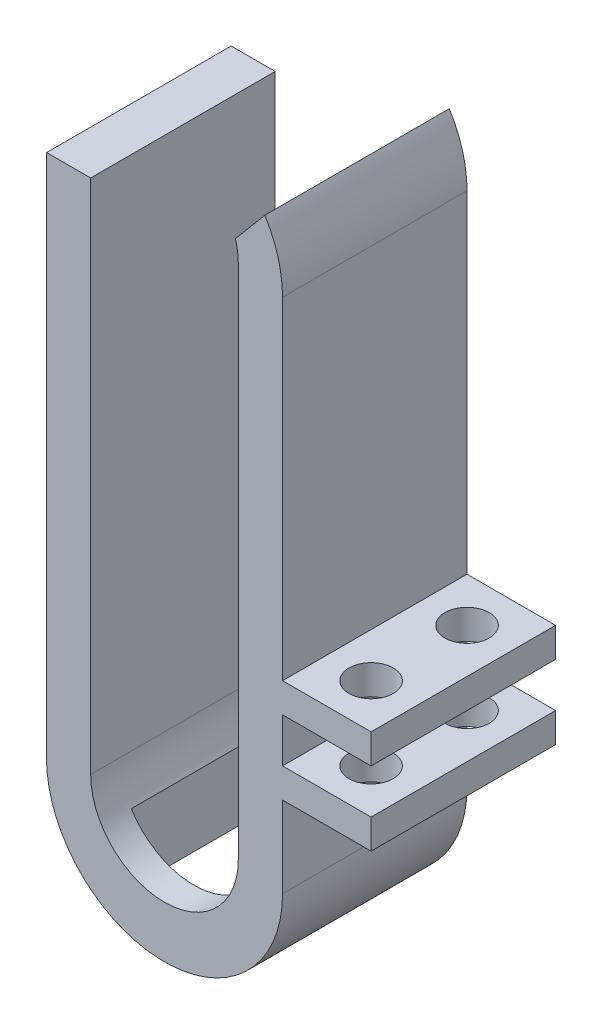
SolidWorks part; units mm, degrees
ref_plane "Front Plane" through (0, 0, 0) normal (0, 0, 1) x (1, 0, 0)
ref_plane "Top Plane" through (0, 0, 0) normal (0, 1, 0) x (1, 0, 0)
ref_plane "Right Plane" through (0, 0, 0) normal (1, 0, 0) x (0, 0, -1)
sketch "Sketch1" plane through (0, 0, 0) normal (0, 0, 1) x (1, 0, 0)
  line L0 (0, 17.5) -> (0, -17.5) construction
  line L1 (5, 17.5) -> (5, -17.5)
  line L2 (-5, 8.5) -> (-5, -17.5)
  line L3 (8, 17) -> (8, -18)
  line L4 (-8, 11.5) -> (-8, -18)
  line L6 (-8, 11.5) -> (-5, 8.5)
  line L9 (-5, 17.5) -> (-5, 8.5)
  line L10 (-8, 17) -> (-8, 11.5)
  line L11 (-6.105, 27.1604) -> (2.0351, 15.5351)
  line L12 (-5, 8.5) -> (2.0351, 15.5351)
  line L13 (-7.9844, 17.5) -> (7.9844, 17.5)
  line L14 (2.0351, 15.5351) -> (9.5686, 24.5132)
  arc A0 (5, 17.5) -> (-5, 17.5) centre (0, 17.5) ccw
  arc A1 (-5, -17.5) -> (5, -17.5) centre (0, -17.5) ccw
  arc A2 (-8, -18) -> (8, -18) centre (0, -18) ccw
  arc A3 (8, 17) -> (-8, 17) centre (0, 17) ccw
  point P2 (0, 0)
  dimension "D4" = 35
  dimension "D7" = 100
  dimension "D8" = 75
  dimension "D1" = 3
  dimension "D2" = 3
  dimension "D3" = 5
  dimension "D5" = 35
  dimension "D6" = 17
extrude "Boss-Extrude1" add sketch "Sketch1" along normal blind 12.5
sketch "Sketch2" plane through (8, 0, 0) normal (1, 0, 0) x (0, 0, -1)
  line L0 (0, 17) -> (0, -18) construction
  line L7 (-12.5, 17) -> (0, 17) construction
  line L8 (-12.5, 17) -> (-12.5, -18) construction
  line L9 (-12.5, -12.5) -> (0, -12.5)
  line L10 (-12.5, -12.5) -> (-12.5, -10.5)
  line L11 (-12.5, -10.5) -> (0, -10.5)
  line L12 (0, -12.5) -> (0, -10.5)
  line L13 (-12.5, -5.5) -> (0, -5.5)
  line L14 (-12.5, -5.5) -> (-12.5, -7.5)
  line L15 (-12.5, -7.5) -> (0, -7.5)
  line L16 (0, -5.5) -> (0, -7.5)
  dimension "D1" = 22.5
  dimension "D2" = 3
  dimension "D3" = 2
  dimension "D4" = 2
extrude "Boss-Extrude2" add sketch "Sketch2" along normal blind 6
sketch "Sketch3" plane through (0, -10.5, 0) normal (0, 1, 0) x (1, 0, 0)
  line L0 (14, 0) -> (8, 0) construction
  line L1 (8, -6.25) -> (14, -6.25) construction
  line L2 (8, 0) -> (8, -12.5) construction
  line L3 (14, 0) -> (14, -12.5) construction
  circle A1 centre (11, -3) radius 1.5
  circle A2 centre (11, -9.5) radius 1.5
  point P10 (11, -9.5)
  dimension "D1" = 3
  dimension "D2" = 3
  dimension "D3" = 3
extrude "Cut-Extrude1" cut sketch "Sketch3" against normal through all both and the other way through all
sketch "Sketch5" plane through (0, 0, 0) normal (0, 1, 0) x (1, 0, 0)
  line L0 (-8, -12.5) -> (-8, 0) construction
  line L1 (-4.25, -2) -> (4.25, -2)
  line L2 (-4.25, -2) -> (-4.25, -10.5)
  line L3 (-4.25, -10.5) -> (4.25, -10.5)
  line L4 (4.25, -2) -> (4.25, -10.5)
  line L7 (5, 0) -> (-5, 0) construction
  dimension "D1" = 8.5
  dimension "D2" = 8.5
  dimension "D3" = 3.75
  dimension "D4" = 2
extrude "Cut-Extrude2" cut sketch "Sketch5" against normal through all
